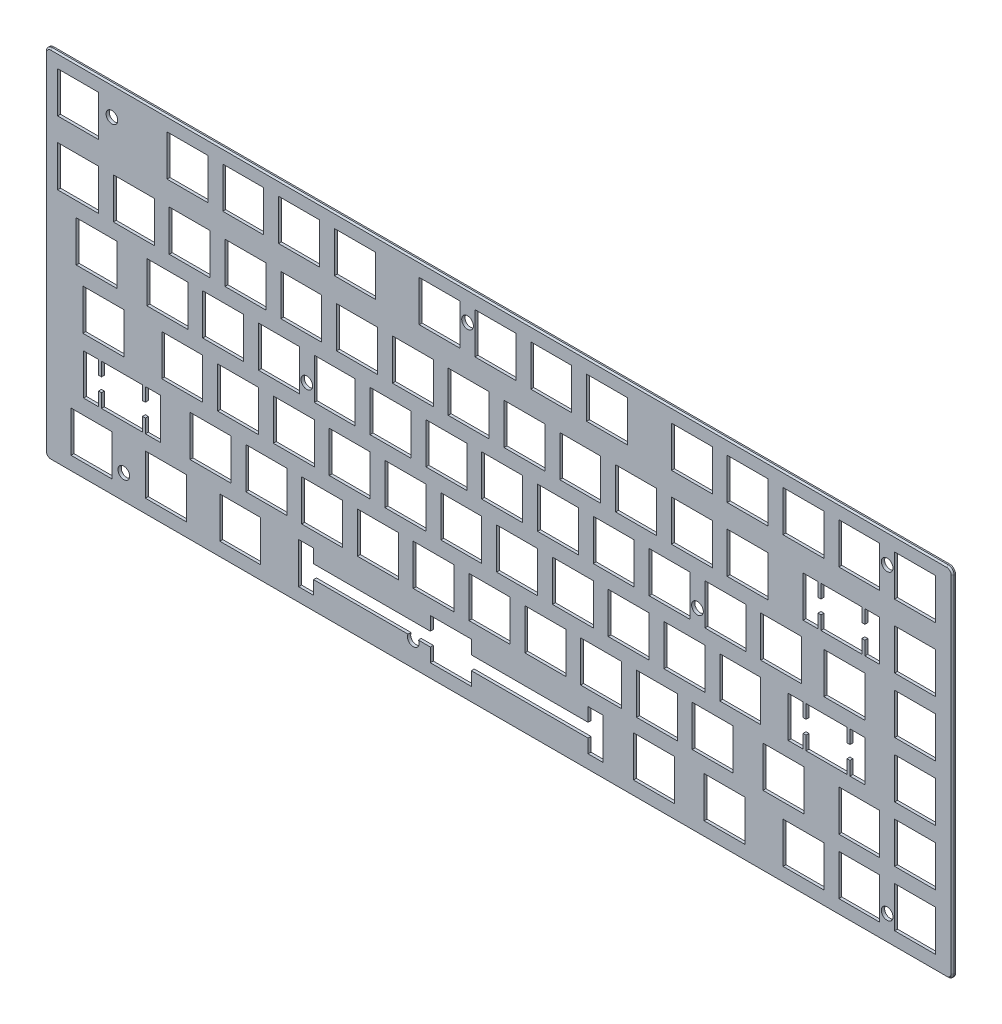
SolidWorks part; units mm, degrees
ref_plane "Alzado" through (0, 0, 0) normal (0, 0, 1) x (1, 0, 0)
ref_plane "Planta" through (0, 0, 0) normal (0, 1, 0) x (1, 0, 0)
ref_plane "Vista lateral" through (0, 0, 0) normal (1, 0, 0) x (0, 0, -1)
sketch "Croquis1" plane through (0, 0, 0) normal (0, 0, 1) x (1, 0, 0)
  line L0 (0, 0) -> (0, 83.5544) construction
  line L1 (-150.876, -60.96) -> (154.94, -60.96)
  line L2 (-152.908, -58.928) -> (-152.908, 58.928)
  line L3 (-150.876, 60.96) -> (154.94, 60.96)
  line L4 (156.972, -58.928) -> (156.972, 58.928)
  line L5 (0, 0) -> (179.8868, 0) construction
  line L6 (-131.318, -55.88) -> (-131.318, -41.91) [skipped]
  line L7 (-144.018, -55.88) -> (-130.048, -55.88)
  line L8 (-144.018, -55.88) -> (-144.018, -41.91)
  line L9 (-144.018, -41.91) -> (-130.048, -41.91)
  line L10 (-130.048, -55.88) -> (-130.048, -41.91)
  line L11 (-131.318, -55.88) -> (-117.348, -55.88) [skipped]
  line L12 (-117.348, -55.88) -> (-117.348, -41.91) [skipped]
  line L13 (-131.318, -41.91) -> (-117.348, -41.91) [skipped]
  line L14 (-118.618, -55.88) -> (-118.618, -41.91)
  line L15 (-118.618, -55.88) -> (-104.648, -55.88)
  line L16 (-104.648, -55.88) -> (-104.648, -41.91)
  line L17 (-118.618, -41.91) -> (-104.648, -41.91)
  line L18 (-105.918, -55.88) -> (-105.918, -41.91) [skipped]
  line L19 (-105.918, -55.88) -> (-91.948, -55.88) [skipped]
  line L20 (-91.948, -55.88) -> (-91.948, -41.91) [skipped]
  line L21 (-105.918, -41.91) -> (-91.948, -41.91) [skipped]
  line L22 (-93.218, -55.88) -> (-93.218, -41.91)
  line L23 (-93.218, -55.88) -> (-79.248, -55.88)
  line L24 (-79.248, -55.88) -> (-79.248, -41.91)
  line L25 (-93.218, -41.91) -> (-79.248, -41.91)
  line L26 (-144.018, -55.88) -> (-131.318, -55.88) construction
  line L27 (-21.336, -55.88) -> (-21.336, -51.2233)
  line L28 (-66.294, -41.91) -> (-61.214, -41.91)
  line L29 (-66.294, -41.91) -> (-66.294, -55.88)
  line L30 (-66.294, -55.88) -> (-61.214, -55.88)
  line L31 (-61.214, -41.91) -> (-61.214, -46.5667)
  line L32 (-61.214, -46.5667) -> (-21.336, -46.5667)
  line L34 (-61.214, -51.2233) -> (-21.336, -51.2233)
  line L36 (-133.604, -36.83) -> (-133.604, -32.1733)
  line L37 (-139.7, -22.86) -> (-134.62, -22.86)
  line L38 (-21.336, -55.88) -> (-7.366, -55.88)
  line L39 (-7.366, -55.88) -> (-7.366, -51.2233)
  line L40 (-21.336, -41.91) -> (-7.366, -41.91)
  line L41 (-14.351, -48.895) -> (-14.351, -69.7624) construction
  line L42 (37.592, -55.88) -> (32.512, -55.88)
  line L43 (32.512, -41.91) -> (32.512, -46.5667)
  line L44 (37.592, -41.91) -> (32.512, -41.91)
  line L45 (37.592, -41.91) -> (37.592, -55.88)
  line L46 (32.512, -51.2233) -> (-7.366, -51.2233)
  line L48 (32.512, -46.5667) -> (-7.366, -46.5667)
  line L50 (137.16, -55.88) -> (151.13, -55.88)
  line L51 (137.16, -55.88) -> (137.16, -41.91)
  line L52 (137.16, -41.91) -> (151.13, -41.91)
  line L53 (151.13, -55.88) -> (151.13, -41.91)
  line L54 (118.11, -55.88) -> (132.08, -55.88)
  line L55 (132.08, -55.88) -> (132.08, -41.91)
  line L56 (118.11, -41.91) -> (132.08, -41.91)
  line L57 (118.11, -55.88) -> (118.11, -41.91)
  line L58 (99.06, -55.88) -> (113.03, -55.88)
  line L59 (113.03, -55.88) -> (113.03, -41.91)
  line L60 (99.06, -41.91) -> (113.03, -41.91)
  line L61 (99.06, -55.88) -> (99.06, -41.91)
  line L62 (118.11, -36.83) -> (132.08, -36.83)
  line L63 (132.08, -36.83) -> (132.08, -22.86)
  line L64 (118.11, -22.86) -> (132.08, -22.86)
  line L65 (118.11, -36.83) -> (118.11, -22.86)
  line L66 (99.06, -36.83) -> (113.03, -36.83) [skipped]
  line L67 (113.03, -36.83) -> (113.03, -22.86) [skipped]
  line L68 (99.06, -22.86) -> (113.03, -22.86) [skipped]
  line L69 (99.06, -36.83) -> (99.06, -22.86) [skipped]
  line L70 (118.11, -17.78) -> (132.08, -17.78) [skipped]
  line L71 (132.08, -17.78) -> (132.08, -3.81) [skipped]
  line L72 (118.11, -3.81) -> (132.08, -3.81) [skipped]
  line L73 (118.11, -17.78) -> (118.11, -3.81) [skipped]
  line L74 (99.06, -17.78) -> (113.03, -17.78) [skipped]
  line L75 (113.03, -17.78) -> (113.03, -3.81) [skipped]
  line L76 (99.06, -3.81) -> (113.03, -3.81) [skipped]
  line L77 (99.06, -17.78) -> (99.06, -3.81) [skipped]
  line L78 (118.11, 1.27) -> (132.08, 1.27) [skipped]
  line L79 (132.08, 1.27) -> (132.08, 15.24) [skipped]
  line L80 (118.11, 15.24) -> (132.08, 15.24) [skipped]
  line L81 (118.11, 1.27) -> (118.11, 15.24) [skipped]
  line L82 (99.06, 1.27) -> (113.03, 1.27) [skipped]
  line L83 (113.03, 1.27) -> (113.03, 15.24) [skipped]
  line L84 (99.06, 15.24) -> (113.03, 15.24) [skipped]
  line L85 (99.06, 1.27) -> (99.06, 15.24) [skipped]
  line L86 (118.11, 20.32) -> (132.08, 20.32) [skipped]
  line L87 (132.08, 20.32) -> (132.08, 34.29) [skipped]
  line L88 (118.11, 34.29) -> (132.08, 34.29) [skipped]
  line L89 (118.11, 20.32) -> (118.11, 34.29) [skipped]
  line L90 (99.06, 20.32) -> (113.03, 20.32) [skipped]
  line L91 (113.03, 20.32) -> (113.03, 34.29) [skipped]
  line L92 (99.06, 34.29) -> (113.03, 34.29) [skipped]
  line L93 (99.06, 20.32) -> (99.06, 34.29) [skipped]
  line L94 (137.16, -36.83) -> (151.13, -36.83)
  line L95 (151.13, -36.83) -> (151.13, -22.86)
  line L96 (137.16, -22.86) -> (151.13, -22.86)
  line L97 (137.16, -36.83) -> (137.16, -22.86)
  line L98 (137.16, -17.78) -> (151.13, -17.78)
  line L99 (151.13, -17.78) -> (151.13, -3.81)
  line L100 (137.16, -3.81) -> (151.13, -3.81)
  line L101 (137.16, -17.78) -> (137.16, -3.81)
  line L102 (137.16, 1.27) -> (151.13, 1.27)
  line L103 (151.13, 1.27) -> (151.13, 15.24)
  line L104 (137.16, 15.24) -> (151.13, 15.24)
  line L105 (137.16, 1.27) -> (137.16, 15.24)
  line L106 (137.16, 20.32) -> (151.13, 20.32)
  line L107 (151.13, 20.32) -> (151.13, 34.29)
  line L108 (137.16, 34.29) -> (151.13, 34.29)
  line L109 (137.16, 20.32) -> (137.16, 34.29)
  line L110 (137.16, -55.88) -> (118.11, -55.88) construction
  line L111 (72.136, -55.88) -> (86.106, -55.88)
  line L112 (86.106, -55.88) -> (86.106, -41.91)
  line L113 (72.136, -41.91) -> (86.106, -41.91)
  line L114 (72.136, -55.88) -> (72.136, -41.91)
  line L115 (48.006, -55.88) -> (61.976, -55.88)
  line L116 (61.976, -55.88) -> (61.976, -41.91)
  line L117 (48.006, -41.91) -> (61.976, -41.91)
  line L118 (48.006, -55.88) -> (48.006, -41.91)
  line L119 (92.202, -36.83) -> (106.172, -36.83)
  line L120 (106.172, -36.83) -> (106.172, -22.86)
  line L121 (92.202, -22.86) -> (106.172, -22.86)
  line L122 (92.202, -36.83) -> (92.202, -22.86)
  line L123 (118.11, -36.83) -> (92.202, -36.83) construction
  line L124 (68.072, -36.83) -> (82.042, -36.83)
  line L125 (82.042, -36.83) -> (82.042, -22.86)
  line L126 (68.072, -22.86) -> (82.042, -22.86)
  line L127 (68.072, -36.83) -> (68.072, -22.86)
  line L128 (92.202, -36.83) -> (68.072, -36.83) construction
  line L129 (49.022, -36.83) -> (62.992, -36.83)
  line L130 (62.992, -36.83) -> (62.992, -22.86)
  line L131 (49.022, -22.86) -> (62.992, -22.86)
  line L132 (49.022, -36.83) -> (49.022, -22.86)
  line L133 (29.972, -36.83) -> (43.942, -36.83)
  line L134 (43.942, -36.83) -> (43.942, -22.86)
  line L135 (29.972, -22.86) -> (43.942, -22.86)
  line L136 (29.972, -36.83) -> (29.972, -22.86)
  line L137 (10.922, -36.83) -> (24.892, -36.83)
  line L138 (24.892, -36.83) -> (24.892, -22.86)
  line L139 (10.922, -22.86) -> (24.892, -22.86)
  line L140 (10.922, -36.83) -> (10.922, -22.86)
  line L141 (-8.128, -36.83) -> (5.842, -36.83)
  line L142 (5.842, -36.83) -> (5.842, -22.86)
  line L143 (-8.128, -22.86) -> (5.842, -22.86)
  line L144 (-8.128, -36.83) -> (-8.128, -22.86)
  line L145 (-27.178, -36.83) -> (-13.208, -36.83)
  line L146 (-13.208, -36.83) -> (-13.208, -22.86)
  line L147 (-27.178, -22.86) -> (-13.208, -22.86)
  line L148 (-27.178, -36.83) -> (-27.178, -22.86)
  line L149 (-46.228, -36.83) -> (-32.258, -36.83)
  line L150 (-32.258, -36.83) -> (-32.258, -22.86)
  line L151 (-46.228, -22.86) -> (-32.258, -22.86)
  line L152 (-46.228, -36.83) -> (-46.228, -22.86)
  line L153 (-65.278, -36.83) -> (-51.308, -36.83)
  line L154 (-51.308, -36.83) -> (-51.308, -22.86)
  line L155 (-65.278, -22.86) -> (-51.308, -22.86)
  line L156 (-65.278, -36.83) -> (-65.278, -22.86)
  line L157 (-84.328, -36.83) -> (-70.358, -36.83)
  line L158 (-70.358, -36.83) -> (-70.358, -22.86)
  line L159 (-84.328, -22.86) -> (-70.358, -22.86)
  line L160 (-84.328, -36.83) -> (-84.328, -22.86)
  line L161 (-103.378, -36.83) -> (-89.408, -36.83)
  line L162 (-89.408, -36.83) -> (-89.408, -22.86)
  line L163 (-103.378, -22.86) -> (-89.408, -22.86)
  line L164 (-103.378, -36.83) -> (-103.378, -22.86)
  line L165 (68.072, -36.83) -> (49.022, -36.83) construction
  line L166 (-61.214, -51.2233) -> (-61.214, -55.88)
  line L167 (-21.336, -46.5667) -> (-21.336, -41.91)
  line L168 (-7.366, -46.5667) -> (-7.366, -41.91)
  line L169 (32.512, -51.2233) -> (32.512, -55.88)
  line L170 (-139.7, -22.86) -> (-139.7, -36.83)
  line L171 (-139.7, -36.83) -> (-134.62, -36.83)
  line L172 (-134.62, -22.86) -> (-134.62, -27.5167)
  line L173 (-134.62, -27.5167) -> (-133.604, -27.5167)
  line L174 (-134.62, -32.1733) -> (-133.604, -32.1733)
  line L175 (-133.604, -36.83) -> (-119.634, -36.83)
  line L176 (-119.634, -36.83) -> (-119.634, -32.1733)
  line L177 (-133.604, -22.86) -> (-119.634, -22.86)
  line L178 (-113.538, -36.83) -> (-118.618, -36.83)
  line L179 (-118.618, -22.86) -> (-118.618, -27.5167)
  line L180 (-113.538, -22.86) -> (-118.618, -22.86)
  line L181 (-113.538, -22.86) -> (-113.538, -36.83)
  line L182 (-118.618, -32.1733) -> (-119.634, -32.1733)
  line L183 (-118.618, -27.5167) -> (-119.634, -27.5167)
  line L184 (-134.62, -32.1733) -> (-134.62, -36.83)
  line L185 (-133.604, -27.5167) -> (-133.604, -22.86)
  line L186 (-119.634, -27.5167) -> (-119.634, -22.86)
  line L187 (-118.618, -32.1733) -> (-118.618, -36.83)
  line L188 (-139.954, -17.78) -> (-125.984, -17.78)
  line L189 (-93.98, -17.78) -> (-80.01, -17.78)
  line L190 (-80.01, -17.78) -> (-80.01, -3.81)
  line L191 (-93.98, -3.81) -> (-80.01, -3.81)
  line L192 (-113.03, -17.78) -> (-99.06, -17.78)
  line L193 (-99.06, -17.78) -> (-99.06, -3.81)
  line L194 (-113.03, -3.81) -> (-99.06, -3.81)
  line L195 (-113.03, -17.78) -> (-113.03, -3.81)
  line L196 (-93.98, -17.78) -> (-93.98, -3.81)
  line L197 (-74.93, -17.78) -> (-60.96, -17.78)
  line L198 (-60.96, -17.78) -> (-60.96, -3.81)
  line L199 (-74.93, -3.81) -> (-60.96, -3.81)
  line L200 (-74.93, -17.78) -> (-74.93, -3.81)
  line L201 (-55.88, -17.78) -> (-41.91, -17.78)
  line L202 (-41.91, -17.78) -> (-41.91, -3.81)
  line L203 (-55.88, -3.81) -> (-41.91, -3.81)
  line L204 (-55.88, -17.78) -> (-55.88, -3.81)
  line L205 (-36.83, -17.78) -> (-22.86, -17.78)
  line L206 (-22.86, -17.78) -> (-22.86, -3.81)
  line L207 (-36.83, -3.81) -> (-22.86, -3.81)
  line L208 (-36.83, -17.78) -> (-36.83, -3.81)
  line L209 (-17.78, -17.78) -> (-3.81, -17.78)
  line L210 (-3.81, -17.78) -> (-3.81, -3.81)
  line L211 (-17.78, -3.81) -> (-3.81, -3.81)
  line L212 (-17.78, -17.78) -> (-17.78, -3.81)
  line L213 (1.27, -17.78) -> (15.24, -17.78)
  line L214 (15.24, -17.78) -> (15.24, -3.81)
  line L215 (1.27, -3.81) -> (15.24, -3.81)
  line L216 (1.27, -17.78) -> (1.27, -3.81)
  line L217 (20.32, -17.78) -> (34.29, -17.78)
  line L218 (34.29, -17.78) -> (34.29, -3.81)
  line L219 (20.32, -3.81) -> (34.29, -3.81)
  line L220 (20.32, -17.78) -> (20.32, -3.81)
  line L221 (39.37, -17.78) -> (53.34, -17.78)
  line L222 (53.34, -17.78) -> (53.34, -3.81)
  line L223 (39.37, -3.81) -> (53.34, -3.81)
  line L224 (39.37, -17.78) -> (39.37, -3.81)
  line L225 (58.42, -17.78) -> (72.39, -17.78)
  line L226 (72.39, -17.78) -> (72.39, -3.81)
  line L227 (58.42, -3.81) -> (72.39, -3.81)
  line L228 (58.42, -17.78) -> (58.42, -3.81)
  line L229 (77.47, -17.78) -> (91.44, -17.78)
  line L230 (91.44, -17.78) -> (91.44, -3.81)
  line L231 (77.47, -3.81) -> (91.44, -3.81)
  line L232 (77.47, -17.78) -> (77.47, -3.81)
  line L233 (-113.03, -17.78) -> (-93.98, -17.78) construction
  line L234 (-125.984, -17.78) -> (-125.984, -3.81)
  line L235 (-139.954, -3.81) -> (-125.984, -3.81)
  line L236 (-139.954, -17.78) -> (-139.954, -3.81)
  line L237 (-113.03, -17.78) -> (-139.954, -17.78) construction
  line L238 (106.934, -17.78) -> (106.934, -13.1233)
  line L239 (100.838, -3.81) -> (105.918, -3.81)
  line L240 (100.838, -3.81) -> (100.838, -17.78)
  line L241 (100.838, -17.78) -> (105.918, -17.78)
  line L242 (105.918, -3.81) -> (105.918, -8.4667)
  line L243 (105.918, -8.4667) -> (106.934, -8.4667)
  line L244 (105.918, -13.1233) -> (106.934, -13.1233)
  line L245 (106.934, -17.78) -> (120.904, -17.78)
  line L246 (120.904, -17.78) -> (120.904, -13.1233)
  line L247 (106.934, -3.81) -> (120.904, -3.81)
  line L248 (127, -17.78) -> (121.92, -17.78)
  line L249 (121.92, -3.81) -> (121.92, -8.4667)
  line L250 (127, -3.81) -> (121.92, -3.81)
  line L251 (127, -3.81) -> (127, -17.78)
  line L252 (121.92, -13.1233) -> (120.904, -13.1233)
  line L253 (121.92, -8.4667) -> (120.904, -8.4667)
  line L254 (105.918, -13.1233) -> (105.918, -17.78)
  line L255 (106.934, -8.4667) -> (106.934, -3.81)
  line L256 (120.904, -8.4667) -> (120.904, -3.81)
  line L257 (121.92, -13.1233) -> (121.92, -17.78)
  line L258 (-118.11, 1.27) -> (-104.14, 1.27)
  line L259 (-104.14, 1.27) -> (-104.14, 15.24)
  line L260 (-118.11, 15.24) -> (-104.14, 15.24)
  line L261 (-118.11, 1.27) -> (-118.11, 15.24)
  line L262 (-99.06, 1.27) -> (-85.09, 1.27)
  line L263 (-85.09, 1.27) -> (-85.09, 15.24)
  line L264 (-99.06, 15.24) -> (-85.09, 15.24)
  line L265 (-99.06, 1.27) -> (-99.06, 15.24)
  line L266 (-80.01, 1.27) -> (-66.04, 1.27)
  line L267 (-66.04, 1.27) -> (-66.04, 15.24)
  line L268 (-80.01, 15.24) -> (-66.04, 15.24)
  line L269 (-80.01, 1.27) -> (-80.01, 15.24)
  line L270 (-60.96, 1.27) -> (-46.99, 1.27)
  line L271 (-46.99, 1.27) -> (-46.99, 15.24)
  line L272 (-60.96, 15.24) -> (-46.99, 15.24)
  line L273 (-60.96, 1.27) -> (-60.96, 15.24)
  line L274 (-41.91, 1.27) -> (-27.94, 1.27)
  line L275 (-27.94, 1.27) -> (-27.94, 15.24)
  line L276 (-41.91, 15.24) -> (-27.94, 15.24)
  line L277 (-41.91, 1.27) -> (-41.91, 15.24)
  line L278 (-22.86, 1.27) -> (-8.89, 1.27)
  line L279 (-8.89, 1.27) -> (-8.89, 15.24)
  line L280 (-22.86, 15.24) -> (-8.89, 15.24)
  line L281 (-22.86, 1.27) -> (-22.86, 15.24)
  line L282 (-3.81, 1.27) -> (10.16, 1.27)
  line L283 (10.16, 1.27) -> (10.16, 15.24)
  line L284 (-3.81, 15.24) -> (10.16, 15.24)
  line L285 (-3.81, 1.27) -> (-3.81, 15.24)
  line L286 (15.24, 1.27) -> (29.21, 1.27)
  line L287 (29.21, 1.27) -> (29.21, 15.24)
  line L288 (15.24, 15.24) -> (29.21, 15.24)
  line L289 (15.24, 1.27) -> (15.24, 15.24)
  line L290 (34.29, 1.27) -> (48.26, 1.27)
  line L291 (48.26, 1.27) -> (48.26, 15.24)
  line L292 (34.29, 15.24) -> (48.26, 15.24)
  line L293 (34.29, 1.27) -> (34.29, 15.24)
  line L294 (53.34, 1.27) -> (67.31, 1.27)
  line L295 (67.31, 1.27) -> (67.31, 15.24)
  line L296 (53.34, 15.24) -> (67.31, 15.24)
  line L297 (53.34, 1.27) -> (53.34, 15.24)
  line L298 (72.39, 1.27) -> (86.36, 1.27)
  line L299 (86.36, 1.27) -> (86.36, 15.24)
  line L300 (72.39, 15.24) -> (86.36, 15.24)
  line L301 (72.39, 1.27) -> (72.39, 15.24)
  line L302 (91.44, 1.27) -> (105.41, 1.27)
  line L303 (105.41, 1.27) -> (105.41, 15.24)
  line L304 (91.44, 15.24) -> (105.41, 15.24)
  line L305 (91.44, 1.27) -> (91.44, 15.24)
  line L306 (113.03, 1.27) -> (127, 1.27)
  line L307 (127, 1.27) -> (127, 15.24)
  line L308 (113.03, 15.24) -> (127, 15.24)
  line L309 (113.03, 1.27) -> (113.03, 15.24)
  line L310 (112.014, 20.32) -> (112.014, 24.9767)
  line L311 (105.918, 34.29) -> (110.998, 34.29)
  line L312 (105.918, 34.29) -> (105.918, 20.32)
  line L313 (105.918, 20.32) -> (110.998, 20.32)
  line L314 (110.998, 34.29) -> (110.998, 29.6333)
  line L315 (110.998, 29.6333) -> (112.014, 29.6333)
  line L316 (110.998, 24.9767) -> (112.014, 24.9767)
  line L317 (112.014, 20.32) -> (125.984, 20.32)
  line L318 (125.984, 20.32) -> (125.984, 24.9767)
  line L319 (112.014, 34.29) -> (125.984, 34.29)
  line L320 (132.08, 20.32) -> (127, 20.32)
  line L321 (127, 34.29) -> (127, 29.6333)
  line L322 (132.08, 34.29) -> (127, 34.29)
  line L323 (132.08, 34.29) -> (132.08, 20.32)
  line L324 (127, 24.9767) -> (125.984, 24.9767)
  line L325 (127, 29.6333) -> (125.984, 29.6333)
  line L326 (110.998, 24.9767) -> (110.998, 20.32)
  line L327 (112.014, 29.6333) -> (112.014, 34.29)
  line L328 (125.984, 29.6333) -> (125.984, 34.29)
  line L329 (127, 24.9767) -> (127, 20.32)
  line L330 (-142.24, 1.27) -> (-128.27, 1.27)
  line L331 (-128.27, 1.27) -> (-128.27, 15.24)
  line L332 (-142.24, 15.24) -> (-128.27, 15.24)
  line L333 (-142.24, 1.27) -> (-142.24, 15.24)
  line L334 (137.16, 42.164) -> (151.13, 42.164)
  line L335 (151.13, 42.164) -> (151.13, 56.134)
  line L336 (137.16, 56.134) -> (151.13, 56.134)
  line L337 (137.16, 42.164) -> (137.16, 56.134)
  line L338 (118.11, 42.164) -> (132.08, 42.164)
  line L339 (132.08, 42.164) -> (132.08, 56.134)
  line L340 (118.11, 56.134) -> (132.08, 56.134)
  line L341 (118.11, 42.164) -> (118.11, 56.134)
  line L342 (99.06, 42.164) -> (113.03, 42.164)
  line L343 (113.03, 42.164) -> (113.03, 56.134)
  line L344 (99.06, 56.134) -> (113.03, 56.134)
  line L345 (99.06, 42.164) -> (99.06, 56.134)
  line L346 (80.01, 42.164) -> (93.98, 42.164)
  line L347 (93.98, 42.164) -> (93.98, 56.134)
  line L348 (80.01, 56.134) -> (93.98, 56.134)
  line L349 (80.01, 42.164) -> (80.01, 56.134)
  line L350 (60.96, 42.164) -> (74.93, 42.164)
  line L351 (74.93, 42.164) -> (74.93, 56.134)
  line L352 (60.96, 56.134) -> (74.93, 56.134)
  line L353 (60.96, 42.164) -> (60.96, 56.134)
  line L354 (60.96, 42.164) -> (74.93, 42.164) [skipped]
  line L355 (74.93, 42.164) -> (74.93, 56.134) [skipped]
  line L356 (60.96, 56.134) -> (74.93, 56.134) [skipped]
  line L357 (60.96, 42.164) -> (60.96, 56.134) [skipped]
  line L358 (41.91, 42.164) -> (55.88, 42.164) [skipped]
  line L359 (55.88, 42.164) -> (55.88, 56.134) [skipped]
  line L360 (41.91, 56.134) -> (55.88, 56.134) [skipped]
  line L361 (41.91, 42.164) -> (41.91, 56.134) [skipped]
  line L362 (22.86, 42.164) -> (36.83, 42.164) [skipped]
  line L363 (36.83, 42.164) -> (36.83, 56.134) [skipped]
  line L364 (22.86, 56.134) -> (36.83, 56.134) [skipped]
  line L365 (22.86, 42.164) -> (22.86, 56.134) [skipped]
  line L366 (3.81, 42.164) -> (17.78, 42.164) [skipped]
  line L367 (17.78, 42.164) -> (17.78, 56.134) [skipped]
  line L368 (3.81, 56.134) -> (17.78, 56.134) [skipped]
  line L369 (3.81, 42.164) -> (3.81, 56.134) [skipped]
  line L370 (-15.24, 42.164) -> (-1.27, 42.164) [skipped]
  line L371 (-1.27, 42.164) -> (-1.27, 56.134) [skipped]
  line L372 (-15.24, 56.134) -> (-1.27, 56.134) [skipped]
  line L373 (-15.24, 42.164) -> (-15.24, 56.134) [skipped]
  line L374 (-34.29, 42.164) -> (-20.32, 42.164) [skipped]
  line L375 (-20.32, 42.164) -> (-20.32, 56.134) [skipped]
  line L376 (-34.29, 56.134) -> (-20.32, 56.134) [skipped]
  line L377 (-34.29, 42.164) -> (-34.29, 56.134) [skipped]
  line L378 (-53.34, 42.164) -> (-39.37, 42.164) [skipped]
  line L379 (-39.37, 42.164) -> (-39.37, 56.134) [skipped]
  line L380 (-53.34, 56.134) -> (-39.37, 56.134) [skipped]
  line L381 (-53.34, 42.164) -> (-53.34, 56.134) [skipped]
  line L382 (-72.39, 42.164) -> (-58.42, 42.164) [skipped]
  line L383 (-58.42, 42.164) -> (-58.42, 56.134) [skipped]
  line L384 (-72.39, 56.134) -> (-58.42, 56.134) [skipped]
  line L385 (-72.39, 42.164) -> (-72.39, 56.134) [skipped]
  line L386 (-91.44, 42.164) -> (-77.47, 42.164) [skipped]
  line L387 (-77.47, 42.164) -> (-77.47, 56.134) [skipped]
  line L388 (-91.44, 56.134) -> (-77.47, 56.134) [skipped]
  line L389 (-91.44, 42.164) -> (-91.44, 56.134) [skipped]
  line L390 (-110.49, 42.164) -> (-96.52, 42.164) [skipped]
  line L391 (-96.52, 42.164) -> (-96.52, 56.134) [skipped]
  line L392 (-110.49, 56.134) -> (-96.52, 56.134) [skipped]
  line L393 (-110.49, 42.164) -> (-110.49, 56.134) [skipped]
  line L394 (-129.54, 42.164) -> (-115.57, 42.164) [skipped]
  line L395 (-115.57, 42.164) -> (-115.57, 56.134) [skipped]
  line L396 (-129.54, 56.134) -> (-115.57, 56.134) [skipped]
  line L397 (-129.54, 42.164) -> (-129.54, 56.134) [skipped]
  line L398 (-148.59, 42.164) -> (-134.62, 42.164) [skipped]
  line L399 (-134.62, 42.164) -> (-134.62, 56.134) [skipped]
  line L400 (-148.59, 56.134) -> (-134.62, 56.134) [skipped]
  line L401 (-148.59, 42.164) -> (-148.59, 56.134) [skipped]
  line L402 (60.96, 20.32) -> (74.93, 20.32)
  line L403 (74.93, 20.32) -> (74.93, 34.29)
  line L404 (60.96, 34.29) -> (74.93, 34.29)
  line L405 (60.96, 20.32) -> (60.96, 34.29)
  line L406 (41.91, 20.32) -> (55.88, 20.32)
  line L407 (55.88, 20.32) -> (55.88, 34.29)
  line L408 (41.91, 34.29) -> (55.88, 34.29)
  line L409 (41.91, 20.32) -> (41.91, 34.29)
  line L410 (22.86, 20.32) -> (36.83, 20.32)
  line L411 (36.83, 20.32) -> (36.83, 34.29)
  line L412 (22.86, 34.29) -> (36.83, 34.29)
  line L413 (22.86, 20.32) -> (22.86, 34.29)
  line L414 (3.81, 20.32) -> (17.78, 20.32)
  line L415 (17.78, 20.32) -> (17.78, 34.29)
  line L416 (3.81, 34.29) -> (17.78, 34.29)
  line L417 (3.81, 20.32) -> (3.81, 34.29)
  line L418 (-15.24, 20.32) -> (-1.27, 20.32)
  line L419 (-1.27, 20.32) -> (-1.27, 34.29)
  line L420 (-15.24, 34.29) -> (-1.27, 34.29)
  line L421 (-15.24, 20.32) -> (-15.24, 34.29)
  line L422 (-34.29, 20.32) -> (-20.32, 20.32)
  line L423 (-20.32, 20.32) -> (-20.32, 34.29)
  line L424 (-34.29, 34.29) -> (-20.32, 34.29)
  line L425 (-34.29, 20.32) -> (-34.29, 34.29)
  line L426 (-53.34, 20.32) -> (-39.37, 20.32)
  line L427 (-39.37, 20.32) -> (-39.37, 34.29)
  line L428 (-53.34, 34.29) -> (-39.37, 34.29)
  line L429 (-53.34, 20.32) -> (-53.34, 34.29)
  line L430 (-72.39, 20.32) -> (-58.42, 20.32)
  line L431 (-58.42, 20.32) -> (-58.42, 34.29)
  line L432 (-72.39, 34.29) -> (-58.42, 34.29)
  line L433 (-72.39, 20.32) -> (-72.39, 34.29)
  line L434 (-91.44, 20.32) -> (-77.47, 20.32)
  line L435 (-77.47, 20.32) -> (-77.47, 34.29)
  line L436 (-91.44, 34.29) -> (-77.47, 34.29)
  line L437 (-91.44, 20.32) -> (-91.44, 34.29)
  line L438 (-110.49, 20.32) -> (-96.52, 20.32)
  line L439 (-96.52, 20.32) -> (-96.52, 34.29)
  line L440 (-110.49, 34.29) -> (-96.52, 34.29)
  line L441 (-110.49, 20.32) -> (-110.49, 34.29)
  line L442 (-129.54, 20.32) -> (-115.57, 20.32)
  line L443 (-115.57, 20.32) -> (-115.57, 34.29)
  line L444 (-129.54, 34.29) -> (-115.57, 34.29)
  line L445 (-129.54, 20.32) -> (-129.54, 34.29)
  line L446 (-148.59, 20.32) -> (-134.62, 20.32)
  line L447 (-134.62, 20.32) -> (-134.62, 34.29)
  line L448 (-148.59, 34.29) -> (-134.62, 34.29)
  line L449 (-148.59, 20.32) -> (-148.59, 34.29)
  line L450 (80.01, 20.32) -> (93.98, 20.32)
  line L451 (93.98, 20.32) -> (93.98, 34.29)
  line L452 (80.01, 34.29) -> (93.98, 34.29)
  line L453 (80.01, 20.32) -> (80.01, 34.29)
  line L458 (-25.146, 42.164) -> (-11.176, 42.164)
  line L459 (-11.176, 42.164) -> (-11.176, 56.134)
  line L460 (-25.146, 56.134) -> (-11.176, 56.134)
  line L461 (-25.146, 42.164) -> (-25.146, 56.134)
  line L462 (-6.096, 42.164) -> (7.874, 42.164)
  line L463 (7.874, 42.164) -> (7.874, 56.134)
  line L464 (-6.096, 56.134) -> (7.874, 56.134)
  line L465 (-6.096, 42.164) -> (-6.096, 56.134)
  line L466 (12.954, 42.164) -> (26.924, 42.164)
  line L467 (26.924, 42.164) -> (26.924, 56.134)
  line L468 (12.954, 56.134) -> (26.924, 56.134)
  line L469 (12.954, 42.164) -> (12.954, 56.134)
  line L470 (32.004, 42.164) -> (45.974, 42.164)
  line L471 (45.974, 42.164) -> (45.974, 56.134)
  line L472 (32.004, 56.134) -> (45.974, 56.134)
  line L473 (32.004, 42.164) -> (32.004, 56.134)
  line L474 (-44.196, 42.164) -> (-30.226, 42.164) [skipped]
  line L475 (-30.226, 42.164) -> (-30.226, 56.134) [skipped]
  line L476 (-44.196, 56.134) -> (-30.226, 56.134) [skipped]
  line L477 (-44.196, 42.164) -> (-44.196, 56.134) [skipped]
  line L478 (-111.252, 42.164) -> (-97.282, 42.164)
  line L479 (-97.282, 42.164) -> (-97.282, 56.134)
  line L480 (-111.252, 56.134) -> (-97.282, 56.134)
  line L481 (-111.252, 42.164) -> (-111.252, 56.134)
  line L482 (-92.202, 42.164) -> (-78.232, 42.164)
  line L483 (-78.232, 42.164) -> (-78.232, 56.134)
  line L484 (-92.202, 56.134) -> (-78.232, 56.134)
  line L485 (-92.202, 42.164) -> (-92.202, 56.134)
  line L486 (-73.152, 42.164) -> (-59.182, 42.164)
  line L487 (-59.182, 42.164) -> (-59.182, 56.134)
  line L488 (-73.152, 56.134) -> (-59.182, 56.134)
  line L489 (-73.152, 42.164) -> (-73.152, 56.134)
  line L490 (-54.102, 42.164) -> (-40.132, 42.164)
  line L491 (-40.132, 42.164) -> (-40.132, 56.134)
  line L492 (-54.102, 56.134) -> (-40.132, 56.134)
  line L493 (-54.102, 42.164) -> (-54.102, 56.134)
  line L494 (-148.59, 42.164) -> (-134.62, 42.164)
  line L495 (-134.62, 42.164) -> (-134.62, 56.134)
  line L496 (-148.59, 56.134) -> (-134.62, 56.134)
  line L497 (-148.59, 42.164) -> (-148.59, 56.134)
  arc A0 (-150.876, -60.96) -> (-152.908, -58.928) centre (-150.876, -58.928) cw
  arc A1 (154.94, -60.96) -> (156.972, -58.928) centre (154.94, -58.928) ccw
  arc A2 (154.94, 60.96) -> (156.972, 58.928) centre (154.94, 58.928) cw
  arc A3 (-152.908, 58.928) -> (-150.876, 60.96) centre (-150.876, 58.928) cw
  point P0 (0, 0)
  point P13 (-144.018, -48.895)
  point P41 (-14.351, -48.895)
  point P43 (-96.393, -29.845)
  point P48 (-14.351, -41.91)
  point P180 (-103.378, -29.845)
  point P202 (-96.393, -22.86)
  point P518 (37.592, -48.895)
  point P521 (156.972, 60.96)
  point P524 (-152.908, 60.96)
  dimension "D88" = 2.032
  dimension "D1" = 309.88
  dimension "D2" = 121.92
  dimension "D3" = 13.97
  dimension "D4" = 13.97
  dimension "D5" = 8.89
  dimension "D6" = 5.08
  dimension "D7" = 152.908
  dimension "D8" = 60.96
  dimension "D9" = 5
  dimension "D10" = 12.7
  dimension "D11" = 5.08
  dimension "D12" = 13.97
  dimension "D13" = 12.954
  dimension "D15" = 4.6567
  dimension "D16" = 4.6567
  dimension "D17" = 39.878
  dimension "D18" = 13.97
  dimension "D19" = 13.97
  dimension "D20" = 4.6567
  dimension "D21" = 4.6567
  dimension "D22" = 13.97
  dimension "D23" = 5.842
  dimension "D26" = 5.08
  dimension "D27" = 5.08
  dimension "D28" = 2
  dimension "D29" = 4.6567
  dimension "D30" = 12.954
  dimension "D31" = 13.97
  dimension "D32" = 13.97
  dimension "D33" = 13.97
  dimension "D34" = 13.97
  dimension "D35" = 10.16
  dimension "D37" = 11.938
  dimension "D39" = 10.16
  dimension "D41" = 5.08
  dimension "D42" = 5.08
  dimension "D43" = 13.97
  dimension "D44" = 1.016
  dimension "D45" = 1.016
  dimension "D46" = 10.16
  dimension "D47" = 5.08
  dimension "D48" = 13.97
  dimension "D51" = 5.08
  dimension "D52" = 11
  dimension "D49" = 13.97
  dimension "D50" = 2
  dimension "D53" = 5.08
  dimension "D54" = 2
  dimension "D55" = 12.954
  dimension "D56" = 10.16
  dimension "D57" = 5.08
  dimension "D58" = 1.016
  dimension "D59" = 13.97
  dimension "D60" = 1.016
  dimension "D61" = 5.08
  dimension "D62" = 12.954
  dimension "D63" = 13.97
  dimension "D64" = 1.016
  dimension "D65" = 34.798
  dimension "D67" = 13.97
  dimension "D68" = 1.016
  dimension "D69" = 5.08
  dimension "D70" = 5.08
  dimension "D71" = 4.6567
  dimension "D72" = 10.16
  dimension "D73" = 4.6567
  dimension "D74" = 4.6567
  dimension "D76" = 10.16
  dimension "D77" = 7.874
  dimension "D79" = 5.08
  dimension "D82" = 5.08
  dimension "D84" = 14.986
  dimension "D86" = 14.986
  dimension "D24" = 3
  dimension "D25" = 5
  dimension "D36" = 2
  dimension "D38" = 2
  dimension "D40" = 10
  dimension "D66" = 12
  dimension "D75" = 2
  dimension "D78" = 5
  dimension "D80" = 13
  dimension "D81" = 2
  dimension "D83" = 2
  dimension "D85" = 2
  dimension "D87" = 2
extrude "Saliente-Extruir1" add sketch "Croquis1" along normal blind 0.9906
chamfer "Chaflán1" distance 0.508 angle 45 8 edges at (-152.908, 0, 0.9906) (2.032, 60.96, 0.9906) (156.972, 0, 0.9906) (2.032, -60.96, 0.9906) (-152.3128, 60.3648, 0.9906) (156.3768, 60.3648, 0.9906) (-152.3128, -60.3648, 0.9906) (156.3768, -60.3648, 0.9906)
hole_wizard "Taladro1" positions "Croquis2" profile "Croquis4" legacy end condition up to next
sketch "Croquis2" plane through (0, 0, 0.9906) normal (0, 0, 1) x (1, 0, 0)
  line L0 (154.94, -60.96) -> (-150.876, -60.96) construction
  line L1 (-152.908, -58.928) -> (-152.908, 58.928) construction
  line L2 (-150.876, 60.96) -> (154.94, 60.96) construction
  line L5 (-11.176, 49.149) -> (-6.096, 49.149) construction
  line L6 (-11.176, 42.164) -> (-11.176, 56.134) construction
  line L7 (-6.096, 56.134) -> (-6.096, 42.164) construction
  line L9 (-66.04, 8.255) -> (-60.96, 8.255) construction
  line L10 (-66.04, 1.27) -> (-66.04, 15.24) construction
  line L11 (-60.96, 15.24) -> (-60.96, 1.27) construction
  line L13 (-21.336, -51.2233) -> (-21.336, -55.88) construction
  line L14 (67.31, 8.255) -> (72.39, 8.255) construction
  line L15 (67.31, 1.27) -> (67.31, 15.24) construction
  line L16 (72.39, 15.24) -> (72.39, 1.27) construction
  line L17 (132.08, 49.149) -> (137.16, 49.149) construction
  line L18 (132.08, 42.164) -> (132.08, 56.134) construction
  line L19 (137.16, 56.134) -> (137.16, 42.164) construction
  point P0 (-125.984, -52.07)
  point P2 (-63.5, 5.842)
  point P4 (-130.048, 51.054)
  point P6 (-8.636, 51.054)
  point P8 (-27.178, -52.07)
  point P32 (-8.636, 49.149)
  point P42 (-63.5, 8.255)
  point P61 (134.62, 51.054)
  point P63 (134.62, -52.07)
  point P65 (69.85, 5.842)
  point P79 (69.85, 8.255)
  point P88 (134.62, 49.149)
  dimension "D1" = 8.89
  dimension "D2" = 26.924
  dimension "D3" = 9.906
  dimension "D4" = 22.86
  dimension "D5" = 66.802
  dimension "D6" = 5.842
sketch "Croquis4" plane through (-125.984, -52.07, 0.9906) normal (1, 0, 0) x (0, -1, 0)
  line L0 (0, 0) -> (0, 0.9906)
  line L1 (0, 0.9906) -> (1.0033, 0.9906)
  line L2 (1.0033, 0.9906) -> (1.0033, 7.5244)
  line L3 (1.0033, 7.5244) -> (1.9939, 0)
  line L4 (1.9939, 0) -> (0, 0)
  line L5 (0, -6.4453) -> (0, 115.525) construction
  line L6 (-1.0033, 7.5244) -> (-1.9939, 0) construction
  dimension "Diámetro" = 2.0066
  dimension "Profundidad" = 0.9906
  dimension "Ángulo de avellanado 1" = 15
  dimension "Diámetro de avellanado 1" = 3.9878
